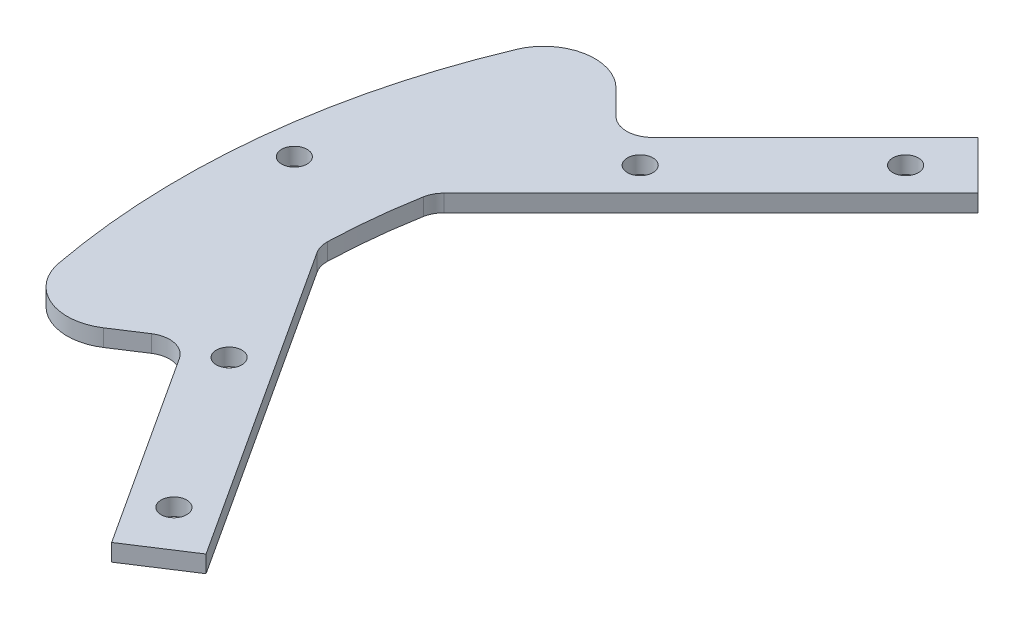
SolidWorks part; units mm, degrees
ref_plane "Front Plane" through (0, 0, 0) normal (0, 0, 1) x (1, 0, 0)
ref_plane "Top Plane" through (0, 0, 0) normal (0, 1, 0) x (1, 0, 0)
ref_plane "Right Plane" through (0, 0, 0) normal (1, 0, 0) x (0, 0, -1)
sketch "Sketch1" plane through (0, 0, 0) normal (0, 1, 0) x (1, 0, 0)
  line L0 (-74.629, 40.6879) -> (-63.6396, 29.6985)
  line L1 (-63.6396, 29.6985) -> (-42.4264, 50.9117)
  line L2 (-42.4264, 50.9117) -> (-36.7696, 45.2548)
  line L3 (-36.7696, 45.2548) -> (-68.725, 13.2994)
  line L5 (-69.9883, 1.28) -> (-45.3751, -36.6211)
  line L6 (-45.3751, -36.6211) -> (-52.0844, -40.9782)
  line L7 (-52.0844, -40.9782) -> (-68.4236, -15.8181)
  line L8 (-68.4236, -15.8181) -> (-81.4577, -24.2825)
  line L9 (0, 0) -> (-85, 0) construction
  line L10 (-43.8406, 43.8406) -> (0, 0) construction
  line L11 (-51.9976, -33.7676) -> (0, 0) construction
  arc A0 (-74.629, 40.6879) -> (-81.4577, -24.2825) centre (0, 0) ccw
  circle A1 centre (-43.8406, 43.8406) radius 1.5
  circle A2 centre (-59.397, 28.2843) radius 1.5
  circle A3 centre (-51.9976, -33.7676) radius 1.5
  circle A4 centre (-63.9796, -15.3169) radius 1.5
  arc A5 (-68.725, 13.2994) -> (-69.9883, 1.28) centre (0, 0) ccw
  dimension "D1" = 85
  dimension "D7" = 3
  dimension "D17" = 70
  dimension "D2" = 8
  dimension "D3" = 4
  dimension "D4" = 4
  dimension "D5" = 24
  dimension "D6" = 24
  dimension "D8" = 6
  dimension "D9" = 22
  dimension "D10" = 22
  dimension "D11" = 6
  dimension "D12" = 4
  dimension "D13" = 4
  dimension "D14" = 45
  dimension "D15" = 33
  dimension "D16" = 66
extrude "Boss-Extrude1" add sketch "Sketch1" along normal blind 2
fillet "Fillet1" radius 6 2 edges at (-74.629, 1, -40.6879) (-81.4577, 1, 24.2825)
fillet "Fillet2" radius 3 4 edges at (-69.9883, 1, -1.28) (-68.725, 1, -13.2994) (-63.6396, 1, -29.6985) (-68.4236, 1, 15.8181)
hole_wizard "Ø3.0 (3) Diameter Hole1" positions "Sketch3" profile "Sketch2" hole size "Ø3.0" standard "ANSI Metric" end condition through all
sketch "Sketch3" plane through (0, 2, 0) normal (0, 1, 0) x (1, 0, 0)
  arc A0 (-78.426, 32.7774) -> (-83.527, -15.7554) centre (0, 0) ccw construction
  point P0 (-80.5344, 8.8849)
  point P3 (-84.5344, 8.8849)
  dimension "D1" = 4
sketch "Sketch2" plane through (-80.5344, 2, -8.8849) normal (1, 0, 0) x (0, 0, 1)
  line L0 (0, 0) -> (0, 2)
  line L1 (0, 2) -> (1.5, 2)
  line L2 (1.5, 2) -> (1.5, 0)
  line L5 (1.5, 0) -> (0, 0)
  line L11 (0, -6.35) -> (0, 107.95) construction
  dimension "Thru Hole Dia." = 3
  dimension "Thru Hole Depth" = 2
